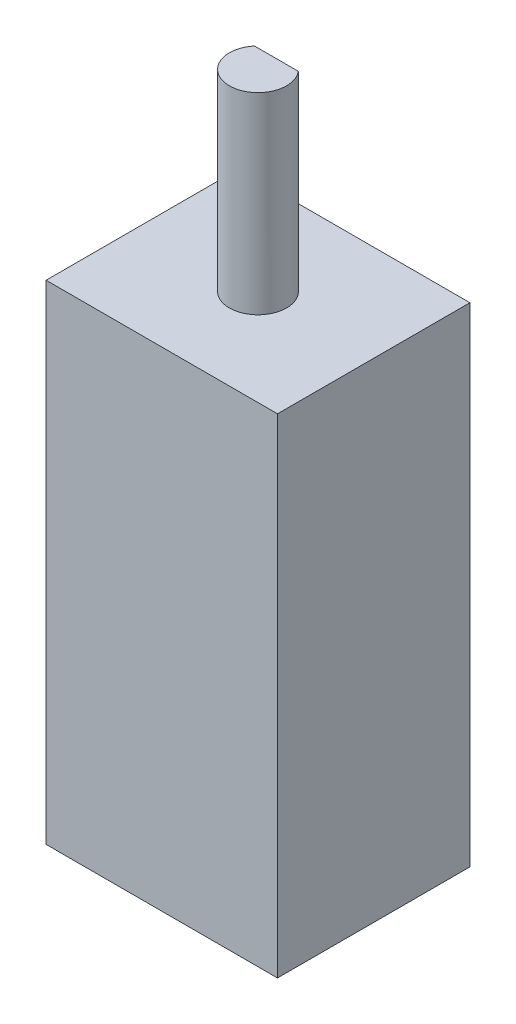
SolidWorks part; units mm, degrees
ref_plane "Front Plane" through (0, 0, 0) normal (0, 0, 1) x (1, 0, 0)
ref_plane "Top Plane" through (0, 0, 0) normal (0, 1, 0) x (1, 0, 0)
ref_plane "Right Plane" through (0, 0, 0) normal (1, 0, 0) x (0, 0, -1)
sketch "Sketch1" plane through (0, 0, 0) normal (0, 0, 1) x (1, 0, 0)
  line L1 (0, 0) -> (12.065, 0)
  line L2 (0, 0) -> (0, 25.4762)
  line L3 (0, 25.4762) -> (12.065, 25.4762)
  line L4 (12.065, 0) -> (12.065, 25.4762)
  dimension "D1" = 12.065
  dimension "D2" = 25.4762
extrude "Boss-Extrude1" add sketch "Sketch1" along normal blind 10.033
sketch "Sketch2" plane through (0, 25.4762, 0) normal (0, 1, 0) x (1, 0, 0)
  line L1 (12.065, 0) -> (0, -10.033) construction
  circle A0 centre (6.0325, -5.0165) radius 1.4922
  dimension "D1" = 2.9845
extrude "Boss-Extrude2" add sketch "Sketch2" along normal blind 10.033
sketch "Sketch3" plane through (0, 35.5092, 0) normal (0, 1, 0) x (1, 0, 0)
  line L0 (4.8901, -4.0564) -> (7.1749, -4.0564)
  line L1 (12.065, 0) -> (0, 0) construction
  circle A0 centre (6.0325, -5.0165) radius 1.4922 construction
  circle A1 centre (6.0325, -5.0165) radius 1.4922 construction
  arc A2 (7.1749, -4.0564) -> (4.8901, -4.0564) centre (6.0325, -5.0165) ccw
  dimension "D1" = 0.9601
extrude "Cut-Extrude1" cut sketch "Sketch3" against normal blind 8.6106
